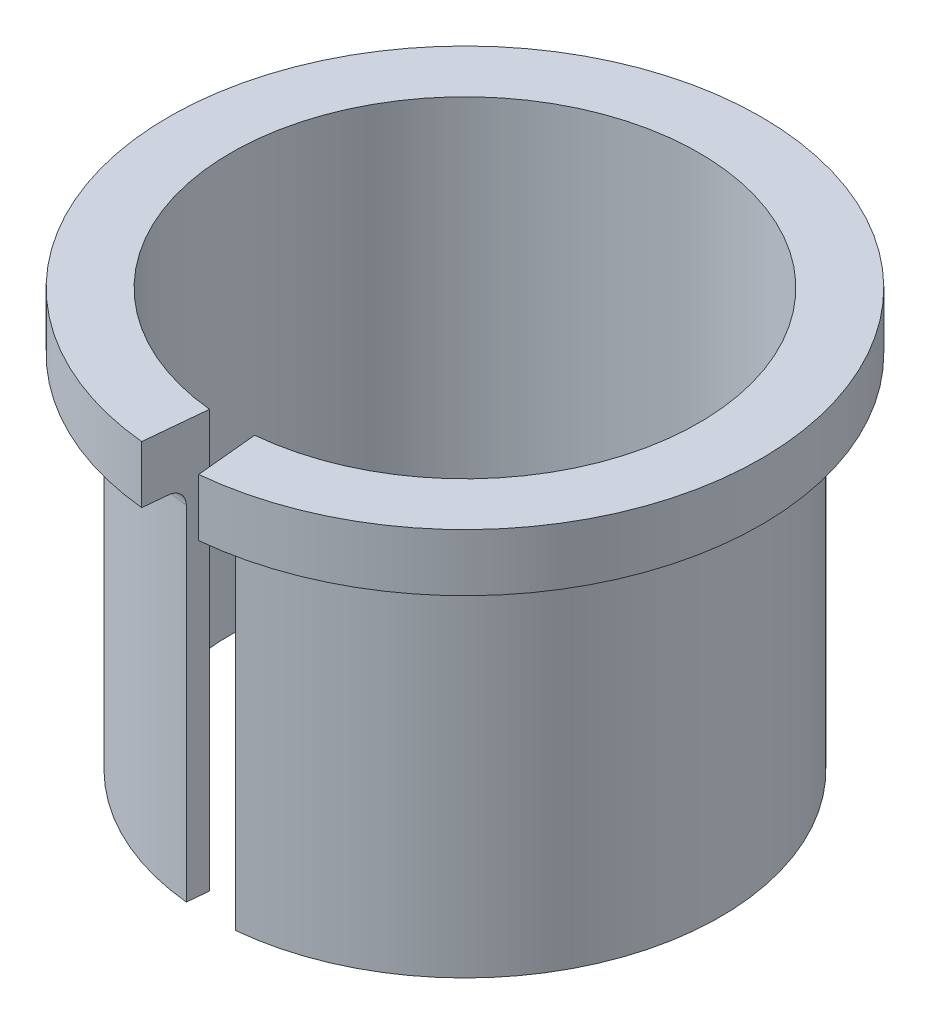
SolidWorks part; units mm, degrees
ref_plane "Front Plane" through (0, 0, 0) normal (0, 0, 1) x (1, 0, 0)
ref_plane "Top Plane" through (0, 0, 0) normal (0, 1, 0) x (1, 0, 0)
ref_plane "Right Plane" through (0, 0, 0) normal (1, 0, 0) x (0, 0, -1)
sketch "Sketch1" plane through (0, 0, 0) normal (0, 1, 0) x (1, 0, 0)
  circle A0 centre (0, 0) radius 15.6
  circle A1 centre (0, 0) radius 14.3
  dimension "D1" = 31.2
  dimension "D2" = 28.6
extrude "Boss-Extrude1" add sketch "Sketch1" along normal blind 22
sketch "Sketch2" plane through (0, 22, 0) normal (0, 1, 0) x (1, 0, 0)
  circle A0 centre (0, 0) radius 14.3 construction
  circle A1 centre (0, 0) radius 14.3
  circle A2 centre (0, 0) radius 18.1
  circle A3 centre (0, 0) radius 15.6 construction
  dimension "D1" = 2.5
extrude "Boss-Extrude2" add sketch "Sketch2" along normal blind 3.5
fillet "Fillet1" radius 1 1 edges at (0, 22, 15.6)
sketch "Sketch3" plane through (0, 25.5, 0) normal (0, 1, 0) x (1, 0, 0)
  line L0 (0, 0) -> (-1.75, -18.1)
  line L1 (-1.75, -18.1) -> (1.75, -18.1)
  line L2 (1.75, -18.1) -> (0, 0)
  line L3 (0, 0) -> (0, -18.1) construction
  circle A0 centre (0, 0) radius 18.1 construction
  point P3 (1.75, -19.6913)
  dimension "D1" = 3.5
extrude "Cut-Extrude1" cut sketch "Sketch3" against normal through all
